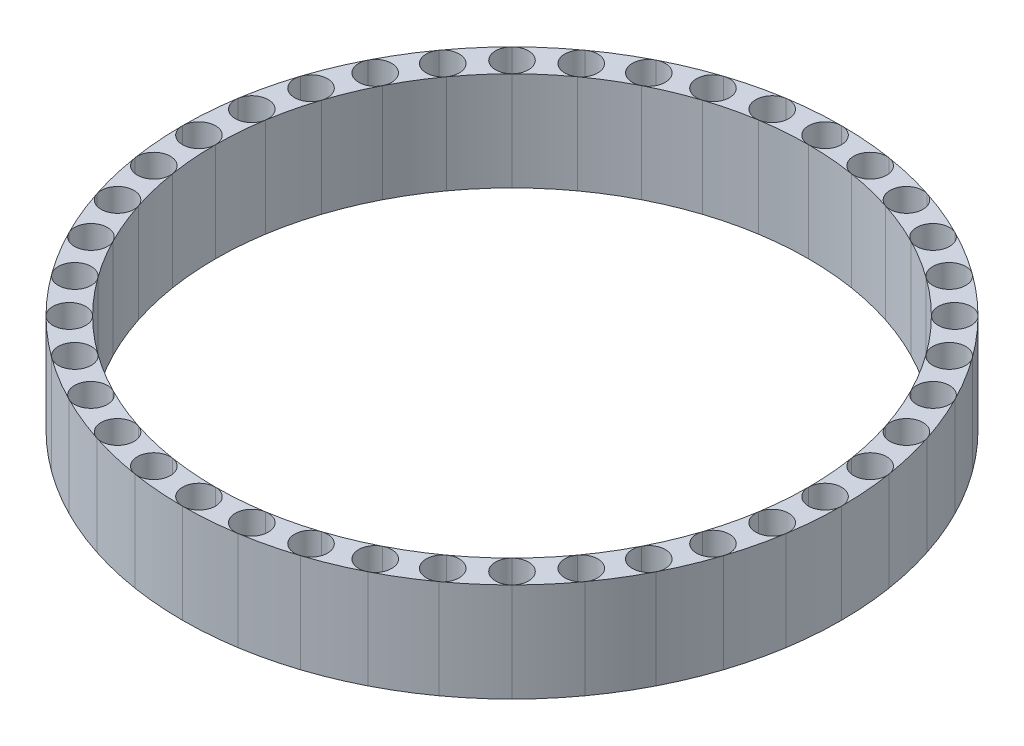
SolidWorks part; units mm, degrees
ref_plane "Front Plane" through (0, 0, 0) normal (0, 0, 1) x (1, 0, 0)
ref_plane "Top Plane" through (0, 0, 0) normal (0, 1, 0) x (1, 0, 0)
ref_plane "Right Plane" through (0, 0, 0) normal (1, 0, 0) x (0, 0, -1)
sketch "Sketch1" plane through (0, 0, 0) normal (0, 1, 0) x (1, 0, 0)
  circle A1 centre (0, 0) radius 127
  dimension "D1" = 254
extrude "Boss-Extrude2" add sketch "Sketch1" along normal blind 38.1
sketch "Sketch5" plane through (0, 38.1, 0) normal (0, 1, 0) x (1, 0, 0)
  circle A0 centre (0, 0) radius 114.3
  dimension "D1" = 228.6
extrude "Cut-Extrude1" cut sketch "Sketch5" against normal through all
sketch "Sketch6" plane through (0, 0, 0) normal (0, -1, 0) x (-1, 0, 0)
  line L0 (0, 0) -> (0, 120.65) construction
  line L1 (0, 0) -> (-127, 0) construction
  line L2 (0, 0) -> (0, -127) construction
  line L3 (0, 0) -> (127, 0) construction
  line L5 (0, 0) -> (89.8026, -89.8026) construction
  line L6 (0, 0) -> (-89.8026, -89.8026) construction
  line L8 (0, 127) -> (0, 114.3) construction
  circle A1 centre (0, 0) radius 127 construction
  circle A3 centre (0, 120.65) radius 6.35
  circle A4 centre (0, 0) radius 114.3 construction
  circle A5 centre (18.8738, 119.1646) radius 6.35
  circle A6 centre (37.2829, 114.745) radius 6.35
  circle A7 centre (54.774, 107.4999) radius 6.35
  circle A8 centre (70.9163, 97.6079) radius 6.35
  circle A9 centre (85.3124, 85.3124) radius 6.35
  circle A10 centre (97.6079, 70.9163) radius 6.35
  circle A11 centre (107.4999, 54.774) radius 6.35
  circle A12 centre (114.745, 37.2829) radius 6.35
  circle A13 centre (119.1646, 18.8738) radius 6.35
  circle A14 centre (120.65, 0) radius 6.35
  circle A15 centre (119.1646, -18.8738) radius 6.35
  circle A16 centre (114.745, -37.2829) radius 6.35
  circle A17 centre (107.4999, -54.774) radius 6.35
  circle A18 centre (97.6079, -70.9163) radius 6.35
  circle A19 centre (85.3124, -85.3124) radius 6.35
  circle A20 centre (70.9163, -97.6079) radius 6.35
  circle A21 centre (54.774, -107.4999) radius 6.35
  circle A22 centre (37.2829, -114.745) radius 6.35
  circle A23 centre (18.8738, -119.1646) radius 6.35
  circle A24 centre (0, -120.65) radius 6.35
  circle A25 centre (-18.8738, -119.1646) radius 6.35
  circle A26 centre (-37.2829, -114.745) radius 6.35
  circle A27 centre (-54.774, -107.4999) radius 6.35
  circle A28 centre (-70.9163, -97.6079) radius 6.35
  circle A29 centre (-85.3124, -85.3124) radius 6.35
  circle A30 centre (-97.6079, -70.9163) radius 6.35
  circle A31 centre (-107.4999, -54.774) radius 6.35
  circle A32 centre (-114.745, -37.2829) radius 6.35
  circle A33 centre (-119.1646, -18.8738) radius 6.35
  circle A34 centre (-120.65, 0) radius 6.35
  circle A35 centre (-119.1646, 18.8738) radius 6.35
  circle A36 centre (-114.745, 37.2829) radius 6.35
  circle A37 centre (-107.4999, 54.774) radius 6.35
  circle A38 centre (-97.6079, 70.9163) radius 6.35
  circle A39 centre (-85.3124, 85.3124) radius 6.35
  circle A40 centre (-70.9163, 97.6079) radius 6.35
  circle A41 centre (-54.774, 107.4999) radius 6.35
  circle A42 centre (-37.2829, 114.745) radius 6.35
  circle A43 centre (-18.8738, 119.1646) radius 6.35
  point P8 (0, 0)
  dimension "D1" = 12.7
  dimension "D2" = 40
  dimension "D3" = 45
  dimension "D4" = 45
  dimension "D5" = 120.65
extrude "Cut-Extrude2" cut sketch "Sketch6" against normal through all
